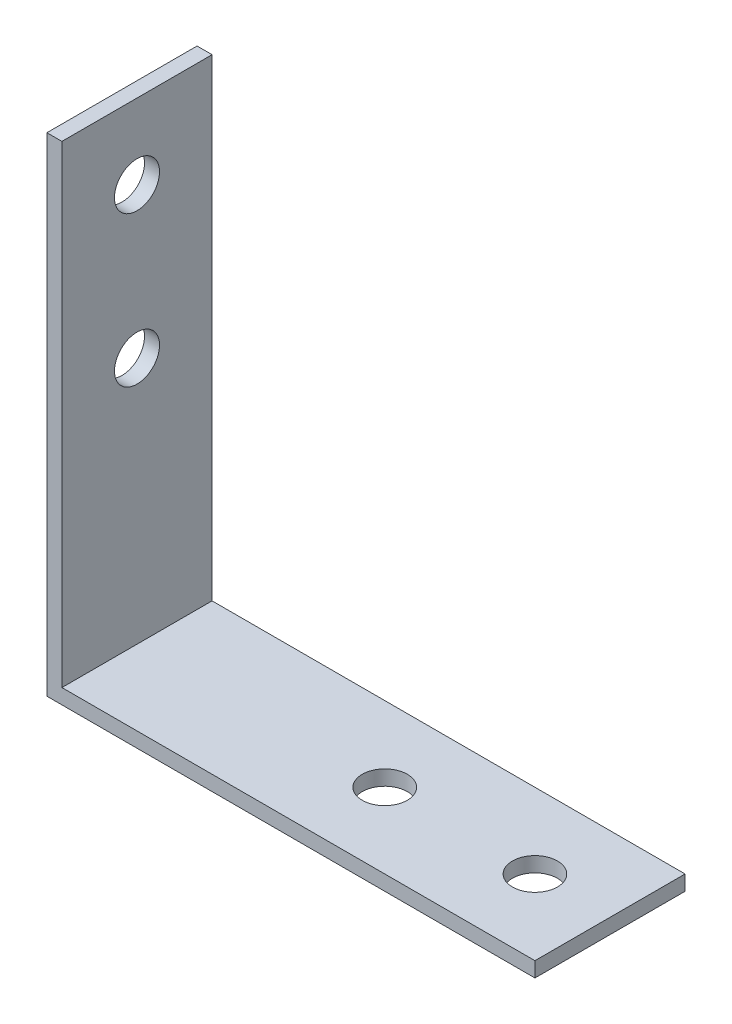
SolidWorks part; units mm, degrees
ref_plane "Front Plane" through (0, 0, 0) normal (0, 0, 1) x (1, 0, 0)
ref_plane "Top Plane" through (0, 0, 0) normal (0, 1, 0) x (1, 0, 0)
ref_plane "Right Plane" through (0, 0, 0) normal (1, 0, 0) x (0, 0, -1)
sketch "Esquisse1" plane through (0, 0, 0) normal (0, 0, 1) x (1, 0, 0)
  line L0 (0, 0) -> (32.5, 0)
  line L1 (32.5, 0) -> (32.5, 1)
  line L2 (32.5, 1) -> (1, 1)
  line L3 (1, 1) -> (1, 32.5)
  line L4 (1, 32.5) -> (0, 32.5)
  line L5 (0, 32.5) -> (0, 0)
  point P7 (19.9506, 1.4043)
  point P8 (9.3566, 30)
  dimension "D1" = 32.5
  dimension "D2" = 1
extrude "Boss.-Extru.1" add sketch "Esquisse1" along normal blind 10
sketch "Esquisse2" plane through (0, 0, 0) normal (-1, 0, 0) x (0, 0, 1)
  line L0 (10, 32.5) -> (0, 32.5) construction
  circle A0 centre (5, 27.5) radius 1.5
  point P4 (5, 32.5)
  dimension "D1" = 3
  dimension "D2" = 5
extrude "Enlèv. mat.-Extru.1" cut sketch "Esquisse2" against normal through all
pattern_linear "Répétition linéaire1" count 2 spacing 10 along (0, -1, 0) of "Enlèv. mat.-Extru.1"
sketch "Esquisse3" plane through (0, 0, 0) normal (0, -1, 0) x (1, 0, 0)
  line L0 (32.5, 10) -> (32.5, 0) construction
  circle A0 centre (27.5, 5) radius 1.5
  point P2 (0, 0)
  point P5 (32.5, 5)
  dimension "D1" = 3
  dimension "D2" = 5
extrude "Enlèv. mat.-Extru.2" cut sketch "Esquisse3" against normal through all
pattern_linear "Répétition linéaire2" count 2 spacing 10 along (-1, 0, 0) of "Enlèv. mat.-Extru.2"
